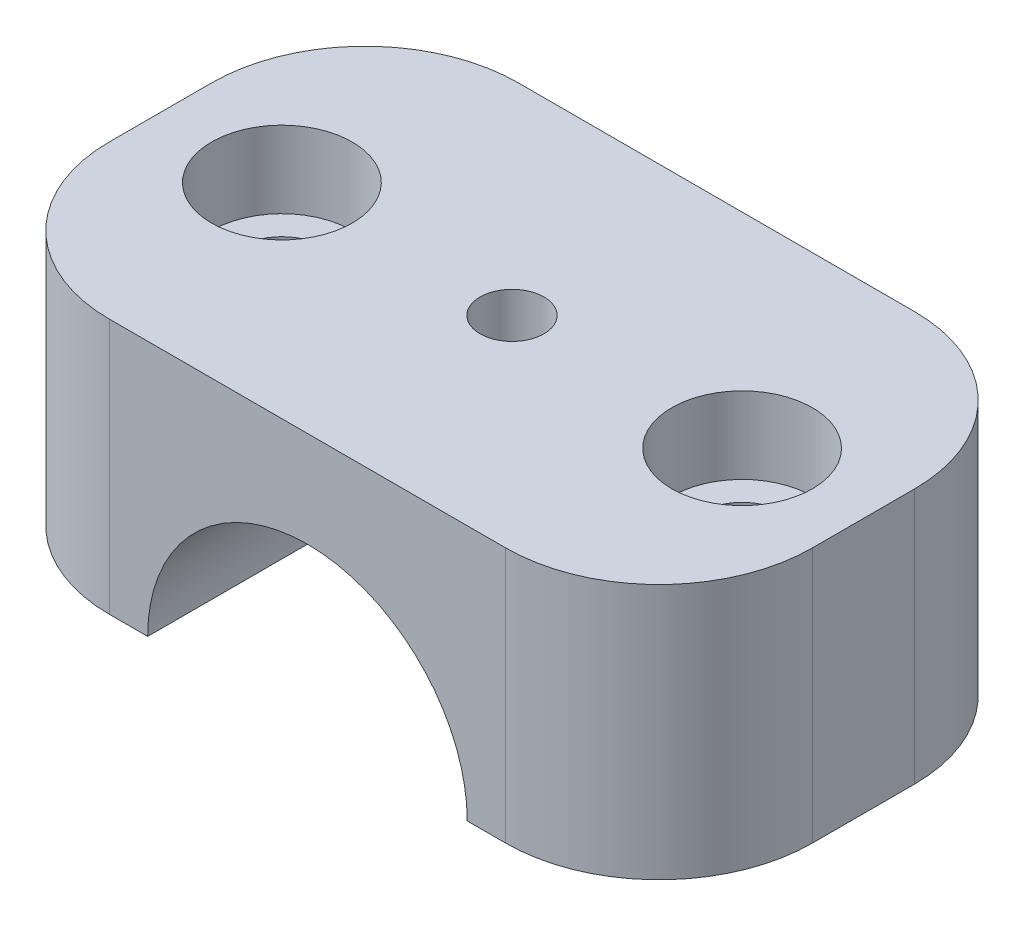
SolidWorks part; units mm, degrees
ref_plane "Front Plane" through (0, 0, 0) normal (0, 0, 1) x (1, 0, 0)
ref_plane "Top Plane" through (0, 0, 0) normal (0, 1, 0) x (1, 0, 0)
ref_plane "Right Plane" through (0, 0, 0) normal (1, 0, 0) x (0, 0, -1)
sketch "Sketch1" plane through (0, 0, 0) normal (0, 0, 1) x (1, 0, 0)
  line L0 (55, 0) -> (-55, 0) construction
  line L1 (-27.5, 0) -> (27.5, 0)
  line L2 (-27.5, 0) -> (-27.5, 20)
  line L3 (-27.5, 20) -> (27.5, 20)
  line L4 (27.5, 0) -> (27.5, 20)
  dimension "D1" = 20
  dimension "D2" = 55
extrude "Boss-Extrude1" add sketch "Sketch1" along normal blind 32
sketch "Sketch2" plane through (0, 0, 32) normal (0, 0, 1) x (1, 0, 0)
  circle A0 centre (0, 0) radius 12.5
  dimension "D1" = 25
extrude "Cut-Extrude1" cut sketch "Sketch2" against normal through all
fillet "Fillet1" radius 12 4 edges at (-27.5, 10, 32) (27.5, 10, 0) (27.5, 10, 32) (-27.5, 10, 0)
hole_wizard "CBORE for M6 SHCS1" positions "Sketch8" profile "Sketch9" counterbore size "M6" standard "ANSI Metric"
sketch "Sketch8" plane through (0, 0, 0) normal (0, 1, 0) x (1, 0, 0)
  point P0 (-16.4175, -15.2535)
sketch "Sketch9" plane through (-16.4175, 0, 15.2535) normal (1, 0, 0) x (0, 0, -1)
  line L0 (0, 0) -> (0, 20)
  line L1 (0, 20) -> (3.3, 20)
  line L3 (3.3, 20) -> (3.3, 6)
  line L4 (3.3, 6) -> (5.5, 6)
  line L5 (5.5, 6) -> (5.5, 0)
  line L7 (5.5, 0) -> (0, 0)
  line L11 (0, -6.35) -> (0, 107.95) construction
  dimension "Thru Hole Dia." = 6.6
  dimension "Thru Hole Depth" = 20
  dimension "C'Bore Dia." = 11
  dimension "C'Bore Depth" = 6
hole_wizard "CBORE for M6 SHCS2" positions "Sketch12" profile "Sketch13" counterbore size "M6" standard "ANSI Metric"
sketch "Sketch12" plane through (0, 20, 0) normal (0, 1, 0) x (1, 0, 0)
  line L4 (27.5, -16) -> (-27.5, -16)
  line L5 (27.5, -20) -> (27.5, -12) construction
  line L6 (-27.5, -20) -> (-27.5, -12) construction
  point P0 (-19.3278, -16)
  point P27 (0, 0)
sketch "Sketch13" plane through (-19.3278, 20, 16) normal (1, 0, 0) x (0, 0, 1)
  line L0 (0, 0) -> (0, 20)
  line L1 (0, 20) -> (3.3, 20)
  line L3 (3.3, 20) -> (3.3, 6)
  line L4 (3.3, 6) -> (5.5, 6)
  line L5 (5.5, 6) -> (5.5, 0)
  line L7 (5.5, 0) -> (0, 0)
  line L11 (0, -6.35) -> (0, 107.95) construction
  dimension "Thru Hole Dia." = 6.6
  dimension "Thru Hole Depth" = 20
  dimension "C'Bore Dia." = 11
  dimension "C'Bore Depth" = 6
hole_wizard "CBORE for M6 SHCS4" positions "Sketch16" profile "Sketch17" counterbore size "M6" standard "ANSI Metric" end condition through all
sketch "Sketch16" plane through (0, 20, 0) normal (0, 1, 0) x (1, 0, 0)
  line L0 (15.5, 0) -> (-15.5, 0) construction
  point P0 (18, -16)
  point P5 (0, 0)
  dimension "D1" = 16
  dimension "D2" = 18
sketch "Sketch17" plane through (18, 20, 16) normal (1, 0, 0) x (0, 0, 1)
  line L0 (0, 0) -> (0, 20)
  line L1 (0, 20) -> (3.3, 20)
  line L3 (3.3, 20) -> (3.3, 6)
  line L4 (3.3, 6) -> (5.5, 6)
  line L5 (5.5, 6) -> (5.5, 0)
  line L7 (5.5, 0) -> (0, 0)
  line L11 (0, -6.35) -> (0, 107.95) construction
  dimension "Thru Hole Dia." = 6.6
  dimension "Thru Hole Depth" = 20
  dimension "C'Bore Dia." = 11
  dimension "C'Bore Depth" = 6
mirror "Mirror2" about plane through (0, 0, 0) normal (1, 0, 0) of "CBORE for M6 SHCS4"
sketch "Sketch18" plane through (0, 20, 0) normal (0, 1, 0) x (1, 0, 0)
  line L0 (0, -11) -> (0, 11) construction
  circle A0 centre (0, -16) radius 2.5
  dimension "D1" = 16
extrude "Cut-Extrude2" cut sketch "Sketch18" against normal through all
